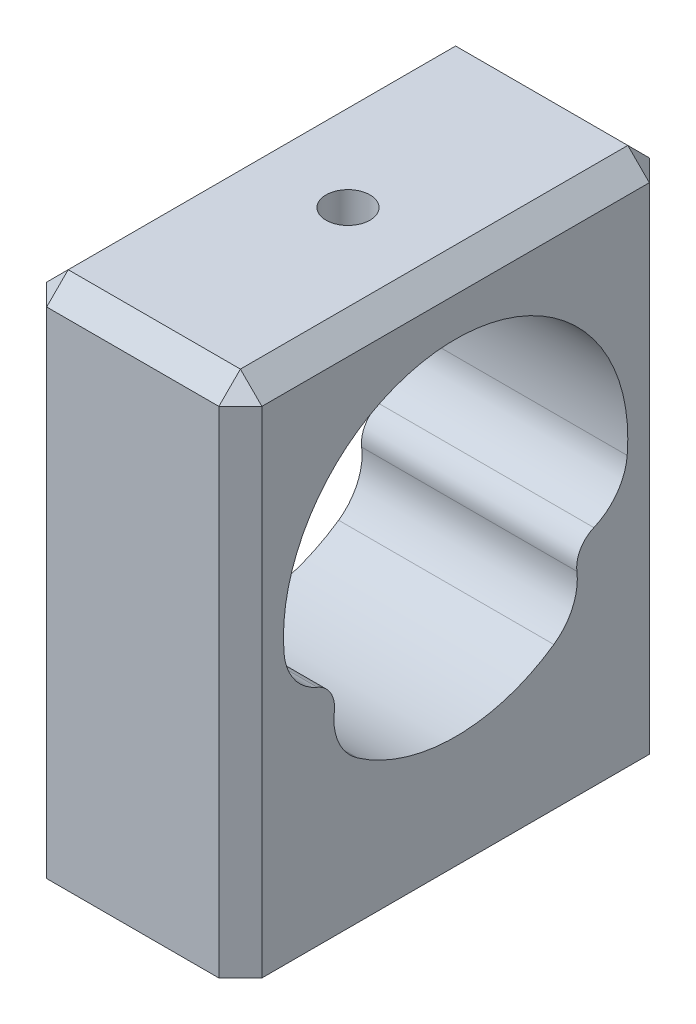
SolidWorks part; units mm, degrees
ref_plane "Front Plane" through (0, 0, 0) normal (0, 0, 1) x (1, 0, 0)
ref_plane "Top Plane" through (0, 0, 0) normal (0, 1, 0) x (1, 0, 0)
ref_plane "Right Plane" through (0, 0, 0) normal (1, 0, 0) x (0, 0, -1)
sketch "Sketch1" plane through (0, 0, 0) normal (1, 0, 0) x (0, 0, -1)
  line L0 (-0.0466, 42.798) -> (-0.0466, -17.202) construction
  line L1 (24.9534, 42.798) -> (-25.0466, 42.798)
  line L2 (24.9534, 42.798) -> (24.9534, -17.202)
  line L3 (24.9534, -17.202) -> (-25.0466, -17.202)
  line L4 (-25.0466, 42.798) -> (-25.0466, -17.202)
  line L5 (-0.0466, 15.818) -> (17.2739, 5.818) construction
  line L6 (-0.0466, 15.818) -> (-17.3671, 5.818) construction
  circle A0 centre (-0.0466, 15.818) radius 20
  circle A1 centre (-0.0466, 15.818) radius 16.74
  arc A2 (18.6684, 8.7647) -> (15.4192, 3.137) centre (17.2739, 5.818) ccw
  arc A3 (-15.5125, 3.137) -> (-18.7616, 8.7647) centre (-17.3671, 5.818) ccw
  arc A4 (19.8837, 14.15) -> (16.0126, 8.8241) centre (13.5558, 14.6796) cw
  arc A5 (14.0399, 5.4072) -> (11.363, -0.6082) centre (7.7405, 4.6071) cw
  arc A6 (-16.1059, 8.8241) -> (-19.977, 14.15) centre (-13.6491, 14.6796) cw
  arc A7 (-14.1331, 5.4072) -> (-11.4563, -0.6082) centre (-7.8337, 4.6071) ccw
  dimension "D3" = 40
  dimension "D5" = 33.48
  dimension "D8" = 6.35
  dimension "D9" = 6.35
  dimension "D10" = 6.35
  dimension "D11" = 6.35
  dimension "D1" = 50
  dimension "D2" = 60
  dimension "D4" = 33.02
  dimension "D6" = 120
  dimension "D7" = 120
extrude "Boss-Extrude1" add sketch "Sketch1" along normal blind 25 contours L1 L4 L3 L2 A0 | A0 A2 | A3 A0 | A0 A4 A2 | A2 A5 A0 | A3 A6 A0 | A7 A3 A0
chamfer "Chamfer1" distance 2.5 angle 45 8 edges at (12.5, 42.798, -24.9534) (0, 42.798, 0.0466) (12.5, 42.798, 25.0466) (25, 42.798, 0.0466) (0, 12.798, -24.9534) (25, 12.798, -24.9534) (0, 12.798, 25.0466) (25, 12.798, 25.0466)
sketch "Sketch2" plane through (0, 42.798, 0) normal (0, 1, 0) x (1, 0, 0)
  line L0 (12.5, 22.4534) -> (12.5, -22.5466) construction
  line L1 (22.5, 22.4534) -> (2.5, 22.4534) construction
  line L2 (2.5, -22.5466) -> (22.5, -22.5466) construction
  line L3 (22.5, -0.0466) -> (2.5, -0.0466) construction
  line L4 (22.5, -22.5466) -> (22.5, 22.4534) construction
  line L5 (2.5, 22.4534) -> (2.5, -22.5466) construction
  point P12 (12.5, -0.0466)
hole_wizard "1/4-20 Tapped Hole1" positions "3DSketch1" profile "Sketch3" tap size "1/4-20" standard "ANSI Inch"
sketch3d "3DSketch1"
  point P0 (12.5, 42.798, 0.0466)
sketch "Sketch3" plane through (12.5, 42.798, 0.0466) normal (1, 0, 0) x (0, 0, 1)
  line L0 (0, 0) -> (0, 6.98)
  line L1 (0, 6.98) -> (2.5527, 6.98)
  line L2 (2.5527, 6.98) -> (2.5527, 0)
  line L5 (2.5527, 0) -> (0, 0)
  line L11 (0, -6.35) -> (0, 107.95) construction
  dimension "Thru Tap Drill Dia." = 5.1054
  dimension "Thru Tap Drill Depth" = 6.98
cosmetic thread "Hole Thread1" parameters "D2"=6.35
sketch "Sketch4" plane through (0, -17.202, 0) normal (0, -1, 0) x (1, 0, 0)
  line L0 (12.5, 25.0466) -> (12.5, -24.9534) construction
  line L1 (22.5, 25.0466) -> (2.5, 25.0466) construction
  line L2 (22.5, -24.9534) -> (2.5, -24.9534) construction
  line L3 (25, 0.0466) -> (0, 0.0466) construction
  line L4 (25, -22.4534) -> (25, 22.5466) construction
  line L5 (0, -22.4534) -> (0, 22.5466) construction
  point P12 (12.5, 15.0466)
  point P13 (12.5, -14.9534)
  dimension "D1" = 10
  dimension "D2" = 10
hole_wizard "1/4 (0.25) Diameter Hole1" positions "3DSketch2" profile "Sketch6" hole size "1/4" standard "ANSI Inch"
sketch3d "3DSketch2"
  point P0 (12.5, -17.202, 15.0466)
  point P3 (12.5, -17.202, -14.9534)
sketch "Sketch6" plane through (12.5, -17.202, 15.0466) normal (1, 0, 0) x (0, 0, -1)
  line L0 (0, 0) -> (0, 11.9077)
  line L1 (0, 11.9077) -> (3.175, 10)
  line L2 (3.175, 10) -> (3.175, 0)
  line L5 (3.175, 0) -> (0, 0)
  line L10 (0, 11.9077) -> (-3.175, 10) construction
  line L11 (0, -6.35) -> (0, 107.95) construction
  dimension "Hole Dia." = 6.35
  dimension "Hole Depth" = 10
  dimension "Drill Angle" = 118
